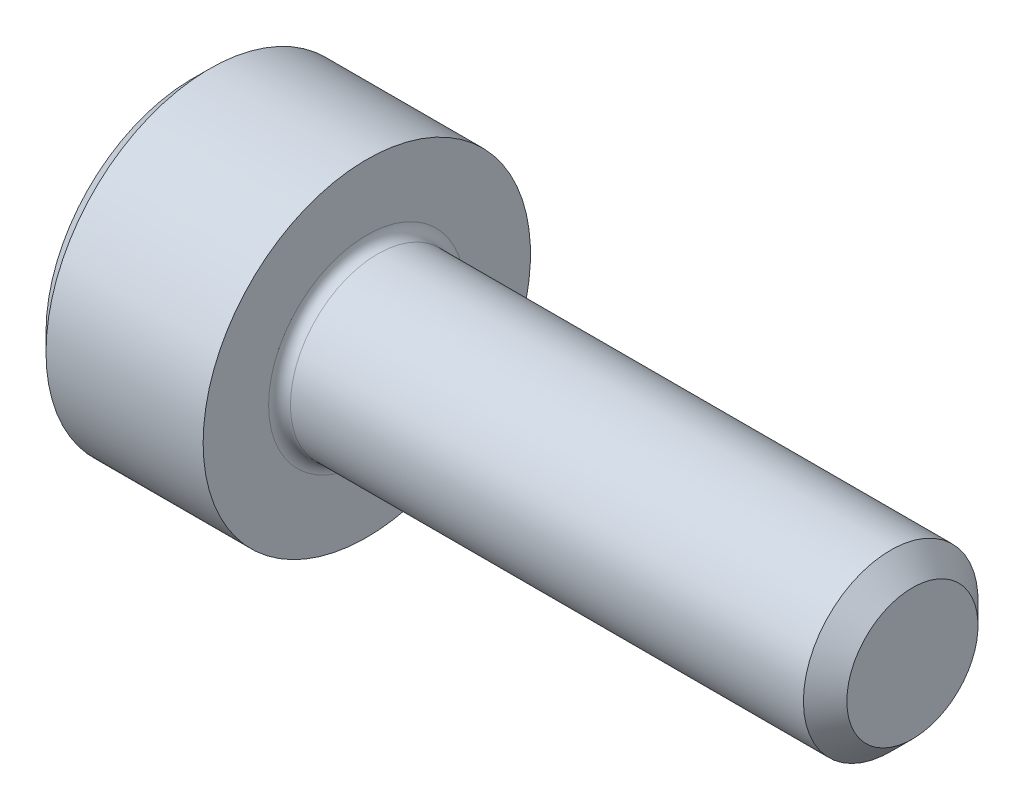
SolidWorks part; units mm, degrees
ref_plane "Plane1" through (0, 0, 0) normal (0, 0, 1) x (1, 0, 0)
ref_plane "Plane2" through (0, 0, 0) normal (0, 1, 0) x (1, 0, 0)
ref_plane "Plane3" through (0, 0, 0) normal (1, 0, 0) x (0, 0, -1)
revolve "Base-Revolve" add sketch "BodySke"
sketch "BodySke" plane through (0, 0, 0) normal (0, 0, 1) x (1, 0, 0)
  line L0 (0, 0) -> (0, 1.34)
  line L1 (0.16, 1.5) -> (1.6, 1.5)
  line L2 (1.6, 1.5) -> (1.6, 0.8)
  line L3 (1.6, 0.8) -> (6.401, 0.8)
  line L4 (6.6, 0.601) -> (6.6, 0)
  line L5 (6.6, 0) -> (0, 0)
  line L6 (-31.75, 0) -> (127, 0) construction
  line L7 (0, 1.34) -> (0.16, 1.5)
  line L8 (6.6, 0.601) -> (6.401, 0.8)
  line L9 (0, -1.34) -> (0.16, -1.5) construction
  line L10 (6.6, -0.601) -> (6.401, -0.8) construction
  line L11 (1.95, 9.525) -> (1.95, 3.175) construction
  line L12 (1.6, 9.525) -> (1.6, 3.175) construction
  line L13 (-43.4, 9.525) -> (-43.4, 3.175) construction
  dimension "Diameter" = 1.6
  dimension "Head_ht" = 1.6
  dimension "Length" = 5
  dimension "Body_ch_ang" = 45
  dimension "Head_dia" = 3
  dimension "Head_ch_ang" = 45
  dimension "Minor_dia" = 1.202
  dimension "Advance" = 0.35
  dimension "Thread_nom" = 5
  dimension "Thread_length" = 50
  dimension "Head_ch_ht" = 0.16
cosmetic thread "ThreadCosmetic" [suppressed]
fillet "Fillet1" radius 0.1 1 edges at (1.6, 0, 0.8)
sketch "Sketch2" plane through (0, 0, 0) normal (0, 0, 1) x (1, 0, 0)
  line L0 (0, 0.7725) -> (0.7, 0.7725)
  line L1 (0.7, 0.7725) -> (1.146, 0)
  line L2 (-31.75, 0) -> (127, 0) construction
  line L3 (1.146, 0) -> (0, 0)
  line L4 (0, 0) -> (0, 0.7725)
  line L5 (0, 1.34) -> (0, -1.34) construction
  line L6 (0, 0) -> (47.625, 0) construction
  line L7 (1.6, -1.5) -> (1.6, 1.5) construction
  dimension "D1" = 0.7725
  dimension "D2" = 60
  dimension "Wall_thickness" = 0.9
revolve "Hex-PreBroach" cut sketch "Sketch2" angle 360 about L6
sketch "Sketch3" plane through (0, 0, 0) normal (-1, 0, 0) x (0, 0.5, 0.866)
  line L0 (0.446, 0.7725) -> (-0.446, 0.7725)
  line L1 (-0.446, 0.7725) -> (-0.892, 0)
  line L2 (0.446, 0.7725) -> (0.892, 0)
  line L3 (0.446, -0.7725) -> (0.892, 0)
  line L4 (0.446, -0.7725) -> (-0.446, -0.7725)
  line L5 (-0.446, -0.7725) -> (-0.892, 0)
  dimension "D1" = 0.7725
  dimension "D2" = 0.7725
  dimension "Hex_size" = 1.545
extrude "Hex" cut sketch "Sketch3" against normal blind 0.7
sketch "Sketch4" plane through (0, 0, 0) normal (-1, 0, 0) x (0, 0, 1)
  line L0 (0, 0) -> (0.9398, 0)
  line L1 (0, 0) -> (6.1484, 3.5498) construction
  line L2 (0, 0) -> (0.4699, 0.8139)
  line L3 (0.7832, 0.2175) -> (0.8962, 0.2828)
  line L4 (0.58, 0.5695) -> (0.693, 0.6348)
  arc A0 (0.7832, 0.2175) -> (0.58, 0.5695) centre (0, 0) ccw
  arc A1 (0.9398, 0) -> (0.8962, 0.2828) centre (0, 0) ccw
  arc A2 (0.4699, 0.8139) -> (0.693, 0.6348) centre (0, 0) cw
  dimension "D1" = 30
  dimension "Spline_n_dim" = 1.6256
  dimension "Spline_m_dim" = 1.8796
  dimension "D2" = 60
  dimension "D3" = 0.2032
  dimension "Spline_p_dim" = 0.4064
extrude "Spline" [suppressed] cut sketch "Sketch4" against normal blind 0.7
pattern_circular "CirPattern1" [suppressed] count 6 every 60
sketch "Sketch5" plane through (0, 0, 0) normal (0, 0, 1) x (1, 0, 0)
  line L0 (-31.75, 0) -> (127, 0) construction
  line L2 (0, 1.34) -> (0, -1.34) construction
  circle A0 centre (0.1, 0) radius 0.005
  dimension "Drilled_hole_dia" = 0.01
  dimension "Drilled_hole_loc" = 0.1
extrude "Hole" [suppressed] cut sketch "Sketch5" against normal through all and the other way through all
pattern_circular "Drilled-4" [suppressed] count 2 every 60
pattern_circular "Drilled-6" [suppressed] count 3 every 60
sketch "ThdSchSke" plane through (0, 0, 0) normal (0, 0, 1) x (1, 0, 0)
  line L0 (1.95, -0.601) -> (1.8107, -0.8)
  line L1 (1.95, -0.601) -> (2.0893, -0.8)
  line L2 (2.0893, -0.8) -> (2.0893, -1)
  line L3 (-3.175, 0) -> (5.1513, 0) construction
  line L5 (2.0893, -1) -> (1.8107, -1)
  line L6 (1.8107, -1) -> (1.8107, -0.8)
  line L7 (0, 1.34) -> (0, -1.34) construction
  dimension "Thread_minor" = 1.202
  dimension "Diameter" = 1.6
  dimension "Start" = 1.95
  dimension "SideAngle" = 55
  dimension "VeeAngle" = 70
  dimension "Overcut" = 2
revolve "ThreadSchematic" [suppressed] cut sketch "ThdSchSke" angle 360 about L3
pattern_linear "ThdSchPat" [suppressed]
equation "\"D2@Sketch3\" = \"Hex_size@Sketch3\" / 2"
equation "\"D1@Sketch3\" = \"Hex_size@Sketch3\" / 2"
equation "\"D1@Sketch2\" = \"Hex_size@Sketch3\" / 2"
equation "\"D3@Sketch4\" = \"Spline_p_dim@Sketch4\" / 2"
equation "\"Thread_minor@ThreadCosmetic\"  =  \"Minor_dia@BodySke\""
equation "\"D2@CirPattern1\" = 360 / \"Num_teeth@CirPattern1\""
equation "\"Wall_thickness@Sketch2\" = \"Head_ht@BodySke\" - \"Key_eng@Hex\""
equation "\"Thread_length@ThreadCosmetic\" = ((sgn( (\"Length@BodySke\" - \"Advance@BodySke\" ) - \"Thread_nom@BodySke\" )-1)*( (\"Length@BodySke\" - \"Advance@BodySke\" ) - \"Thread_nom@BodySke\" ))/-2+ \"Thread_nom@BodySke\""
equation "\"Thread_minor@ThdSchSke\" = \"Minor_dia@BodySke\""
equation "\"Diameter@ThdSchSke\" = \"Diameter@BodySke\""
equation "\"Overcut@ThdSchSke\" = \"Diameter@BodySke\" * 1.25"
equation "\"Start@ThdSchSke\" = \"Head_ht@BodySke\" + \"Length@BodySke\" - \"Thread_length@ThreadCosmetic\"  '---Non-countersunk---"
equation "\"Num_threads@ThdSchPat\" = int( \"Thread_length@ThreadCosmetic\" / \"Advance@BodySke\" + 0.999 )  + 1"
equation "\"Advance@ThdSchPat\" = \"Thread_length@ThreadCosmetic\" /  (\"Num_threads@ThdSchPat\" - 1) 'relax it"
equation "\"Num_threads@ThdSchPat\" = \"Num_threads@ThdSchPat\" - sgn( \"Num_threads@ThdSchPat\" - 1) '---chamfered tips only---"
